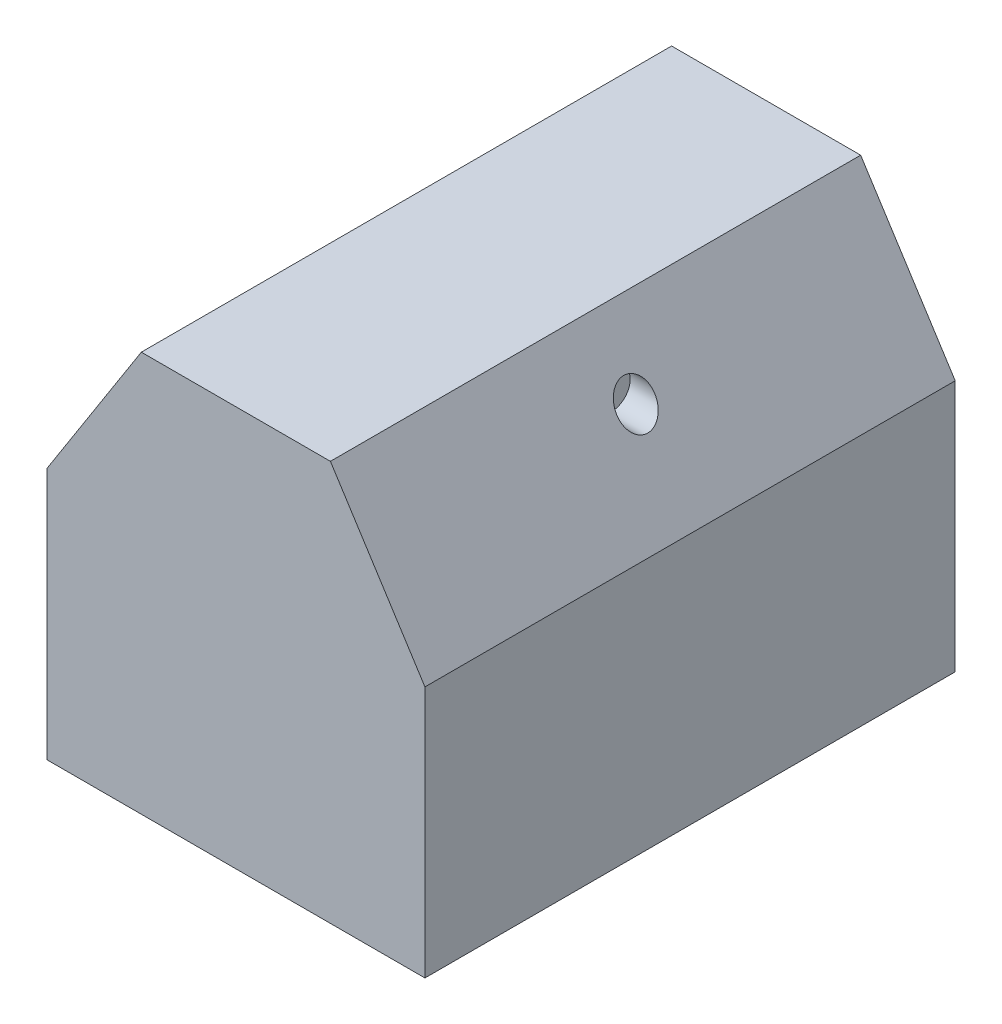
SolidWorks part; units mm, degrees
ref_plane "Plano frontal" through (0, 0, 0) normal (0, 0, 1) x (1, 0, 0)
ref_plane "Plano superior" through (0, 0, 0) normal (0, 1, 0) x (1, 0, 0)
ref_plane "Plano direito" through (0, 0, 0) normal (1, 0, 0) x (0, 0, -1)
sketch "Esboço1" plane through (0, 0, 0) normal (0, 0, 1) x (1, 0, 0)
  line L0 (-60, 0) -> (60, 0)
  line L1 (60, 0) -> (60, 80)
  line L2 (60, 80) -> (30, 127)
  line L3 (30, 127) -> (-30, 127)
  line L4 (0, 0) -> (0, 127) construction
  line L5 (-60, 80) -> (-30, 127)
  line L6 (-60, 0) -> (-60, 80)
  dimension "D1" = 120
  dimension "D2" = 127
  dimension "D3" = 60
  dimension "D4" = 80
extrude "Ressalto-extrusão1" add sketch "Esboço1" along normal mid plane 168.275
sketch "Esboço2" plane through (0, 0, 0) normal (1, 0, 0) x (0, 0, -1)
  line L0 (0, 107) -> (0, 127) construction
  line L1 (-84.1375, 127) -> (84.1375, 127) construction
  circle A0 centre (0, 107) radius 6
  dimension "D1" = 12
  dimension "D2" = 20
extrude "Corte-extrusão1" cut sketch "Esboço2" against normal through all from offset 35 offset against normal yes
mirror "Espelhar1" about plane through (0, 0, 0) normal (1, 0, 0) of "Corte-extrusão1"
